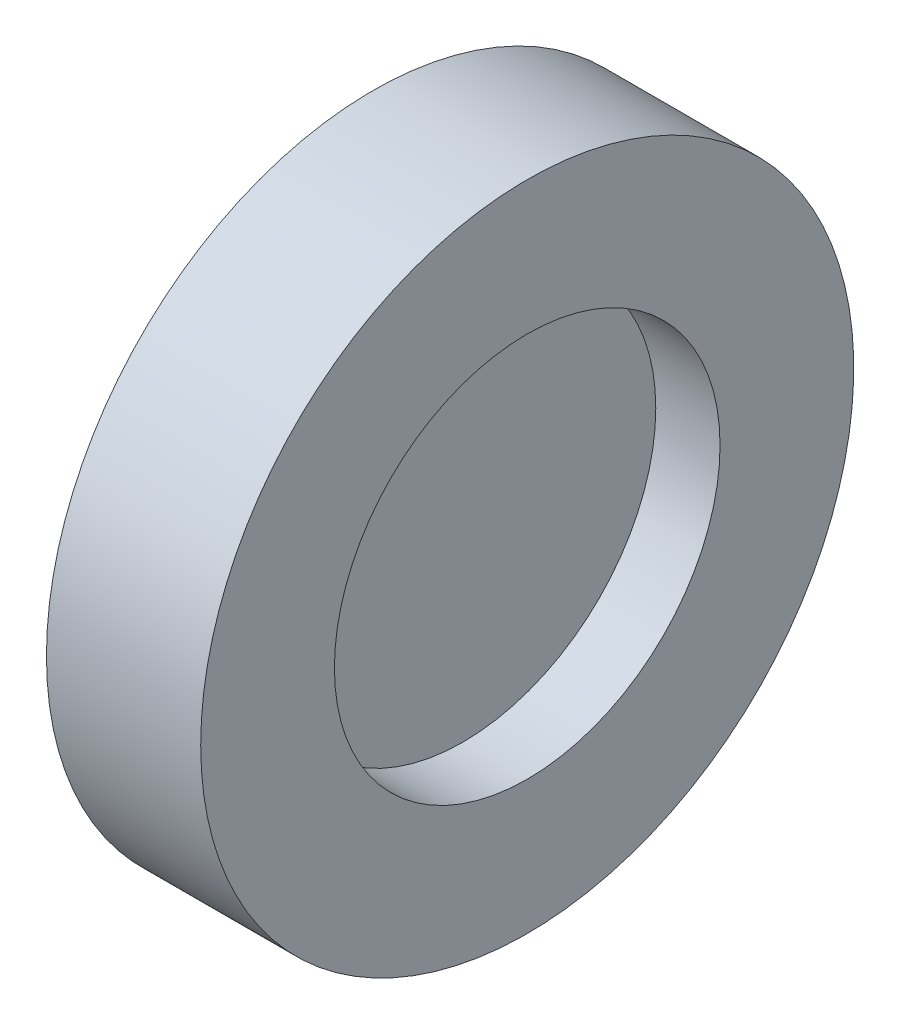
SolidWorks part; units mm, degrees
ref_plane "前视基准面" through (0, 0, 0) normal (0, 0, 1) x (1, 0, 0)
ref_plane "上视基准面" through (0, 0, 0) normal (0, 1, 0) x (1, 0, 0)
ref_plane "右视基准面" through (0, 0, 0) normal (1, 0, 0) x (0, 0, -1)
sketch "草图1" plane through (0, 0, 0) normal (0, 0, 1) x (1, 0, 0)
  line L0 (-0.5, 7.5) -> (-0.5, 0)
  line L2 (-0.5, 7.5) -> (0.5, 7.5)
  line L3 (-0.5, 0) -> (0.5, 0)
  line L4 (0.5, 7.5) -> (0.5, 0)
revolve "旋转2" add sketch "草图1" angle 360 about L3
sketch "草图4" plane through (0, 0, 0) normal (0, 0, 1) x (1, 0, 0)
  line L0 (-3, 12.7) -> (3, 12.7)
  line L1 (3, 12.7) -> (3, 7.5)
  line L2 (3, 7.5) -> (-3, 7.5)
  line L3 (0.5, 7.5) -> (-0.5, 7.5) construction
  line L4 (-3, 7.5) -> (-3, 12.7)
  line L5 (0, 7.5) -> (0, 12.7) construction
  line L6 (-1.6142, 0) -> (1.5903, 0) construction
revolve "旋转3" add sketch "草图4" angle 360 about L6
equation "\"D1@草图4\"=\"D1@草图1\""
